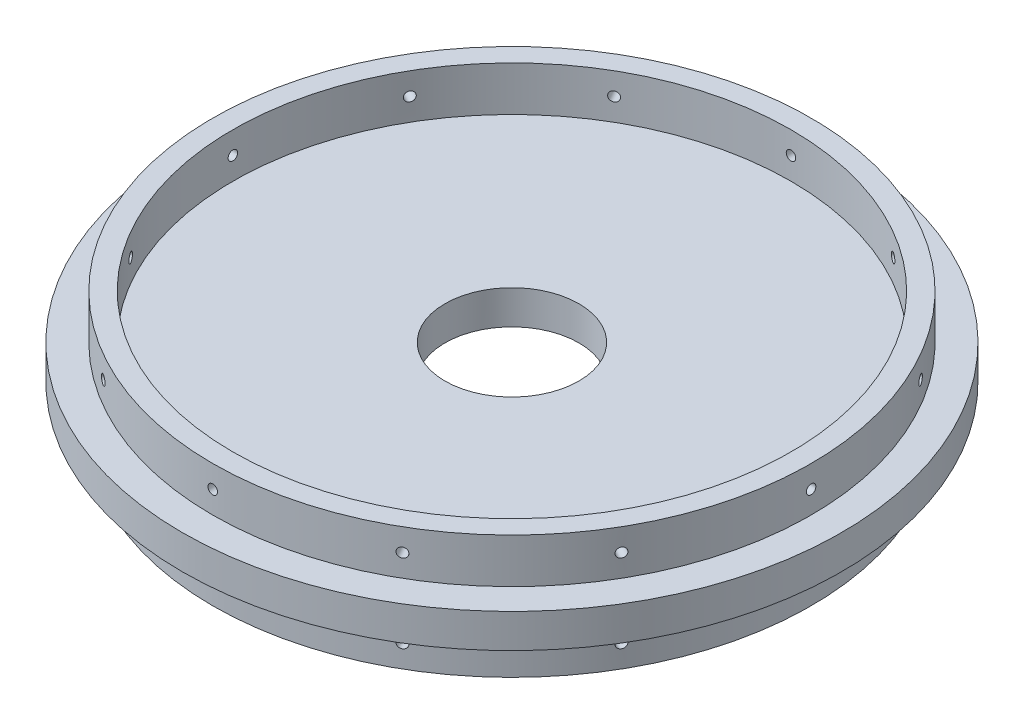
SolidWorks part; units mm, degrees
material "6061-T6 (SS)"
ref_plane "Front Plane" through (0, 0, 0) normal (0, 0, 1) x (1, 0, 0)
ref_plane "Top Plane" through (0, 0, 0) normal (0, 1, 0) x (1, 0, 0)
ref_plane "Right Plane" through (0, 0, 0) normal (1, 0, 0) x (0, 0, -1)
sketch "Sketch1" plane through (0, 0, 0) normal (0, 1, 0) x (1, 0, 0)
  circle A0 centre (0, 0) radius 93.726
  dimension "D1" = 187.452
extrude "Boss-Extrude1" add sketch "Sketch1" along normal mid plane 9.652
sketch "Sketch2" plane through (0, 0, 0) normal (0, 0, 1) x (1, 0, 0)
  line L0 (0, -18.3275) -> (0, 20.8308) construction
  line L1 (0, -4.826) -> (-25.4, -4.826)
  line L2 (-93.726, -4.826) -> (93.726, -4.826) construction
  line L3 (0, -4.826) -> (0, 1.27)
  spline S0 degree 3 poles (0, 1.27) (-5.1197, 1.5129) (-13.6852, -0.4966) (-22.1585, -2.9398) (-25.4, -4.826) knots 0 0 0 0 0.575799 1 1 1 1
  dimension "D1" = 25.4
  dimension "D2" = 6.096
revolve "Cut-Revolve1" [suppressed] cut sketch "Sketch2" angle 360 about L0
sketch "Sketch4" plane through (0, 4.826, 0) normal (0, 1, 0) x (1, 0, 0)
  circle A0 centre (0, 0) radius 85.09
  circle A1 centre (0, 0) radius 79.375
  dimension "D1" = 170.18
  dimension "D2" = 158.75
extrude "Boss-Extrude2" add sketch "Sketch4" along normal blind 12.7
ref_plane "Plane1" through (0, 0, -85.09) normal (0, 0, -1) x (-1, 0, 0)
sketch "Sketch5" plane through (0, 0, -85.09) normal (0, 0, -1) x (-1, 0, 0)
  line L0 (0, 19.2786) -> (0, -19.2786) construction
  line L1 (79.375, 17.526) -> (-79.375, 17.526) construction
  circle A0 centre (0, 11.176) radius 1.3525
  dimension "D1" = 2.7051
  dimension "D2" = 6.35
extrude "Cut-Extrude2" cut sketch "Sketch5" against normal blind 12.7
pattern_circular "CirPattern1" count 12 over 360 about axis through (0, 17.526, 0) along (0, -1, 0) of "Cut-Extrude2"
mirror "Mirror2" about plane through (0, 0, 0) normal (0, 1, 0) of "CirPattern1", "Cut-Extrude2", "Boss-Extrude2"
sketch "Sketch6" plane through (0, 4.826, 0) normal (0, 1, 0) x (1, 0, 0)
  line L0 (-63.5, 0) -> (-69.85, 0)
  line L1 (0, -69.85) -> (0, -63.5)
  line L2 (0, -19.2786) -> (0, 19.2786) construction
  arc A0 (-69.85, 0) -> (0, -69.85) centre (0, 0) ccw
  arc A1 (-63.5, 0) -> (0, -63.5) centre (0, 0) ccw
  dimension "D1" = 69.85
  dimension "D2" = 63.5
  dimension "D3" = 90
extrude "Cut-Extrude3" [suppressed] cut sketch "Sketch6" against normal up to surface (9.652 mm away)
sketch "Sketch7" plane through (0, -4.826, 0) normal (0, -1, 0) x (1, 0, 0)
  circle A0 centre (0, 0) radius 19.05
  dimension "D1" = 38.1
extrude "Cut-Extrude4" cut sketch "Sketch7" against normal through all
